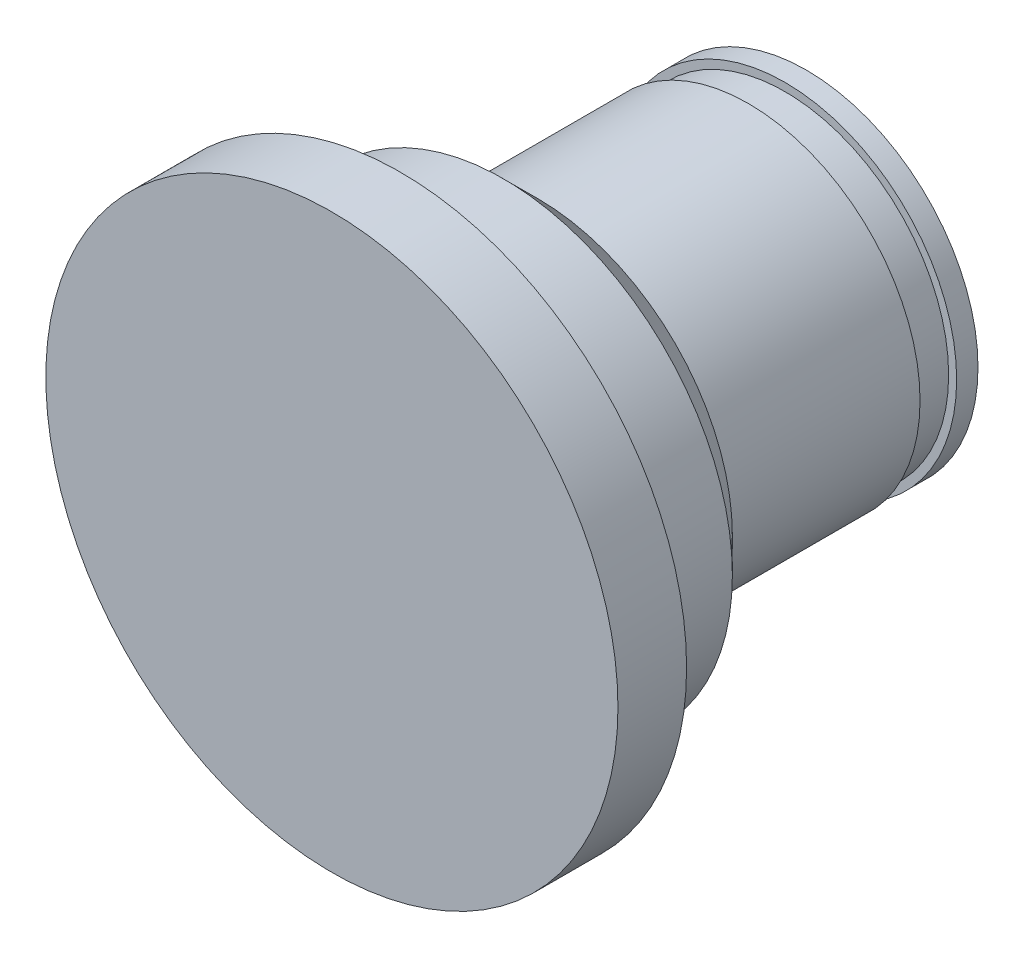
SolidWorks part; units mm, degrees
ref_plane "Front Plane" through (0, 0, 0) normal (0, 0, 1) x (1, 0, 0)
ref_plane "Top Plane" through (0, 0, 0) normal (0, 1, 0) x (1, 0, 0)
ref_plane "Right Plane" through (0, 0, 0) normal (1, 0, 0) x (0, 0, -1)
sketch "Sketch1" plane through (0, 0, 0) normal (0, 1, 0) x (1, 0, 0)
  line L0 (0, 0) -> (0, 52.8705) construction
  line L1 (0, 0) -> (12.5, 0)
  line L2 (12.5, 0) -> (12.5, 3)
  line L3 (12.5, 3) -> (10, 3)
  line L4 (10, 3) -> (10, 9)
  line L5 (10, 9) -> (7.5, 9)
  line L6 (7.5, 9) -> (7.5, 18.2)
  line L7 (7.5, 21) -> (0, 21)
  line L8 (0, 21) -> (0, 0)
  line L9 (7.5, 18.2) -> (7.15, 18.2)
  line L10 (7.15, 18.2) -> (7.15, 19.8)
  line L11 (7.15, 19.8) -> (7.5, 19.8)
  line L12 (7.5, 19.8) -> (7.5, 21)
  dimension "D1" = 12.5
  dimension "D2" = 3
  dimension "D3" = 2.5
  dimension "D4" = 6
  dimension "D5" = 2.5
  dimension "D6" = 12
  dimension "D7" = 1.6
  dimension "D8" = 0.35
  dimension "D9" = 9.2
revolve "Revolve1" add sketch "Sketch1" angle 360 about L0
chamfer "Chamfer1" distance 1 angle 15 1 edges at (7.5, 0, -21)
chamfer "Chamfer2" distance 1.5 angle 45 1 edges at (10, 0, -9)
